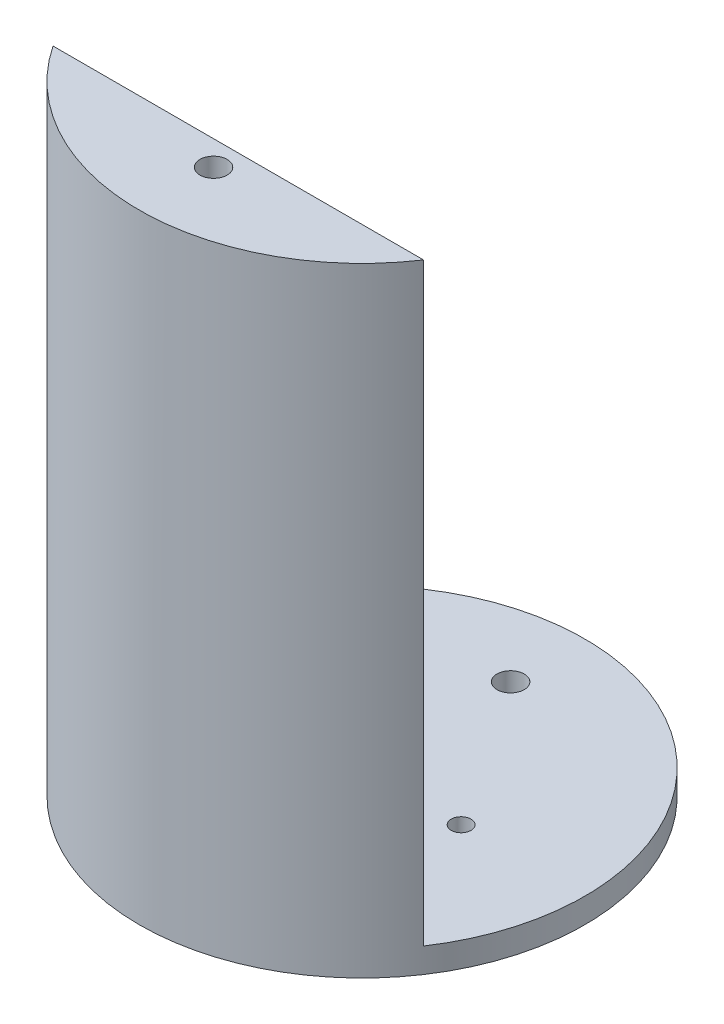
SolidWorks part; units mm, degrees
ref_plane "Front Plane" through (0, 0, 0) normal (0, 0, 1) x (1, 0, 0)
ref_plane "Top Plane" through (0, 0, 0) normal (0, 1, 0) x (1, 0, 0)
ref_plane "Right Plane" through (0, 0, 0) normal (1, 0, 0) x (0, 0, -1)
sketch "Sketch1" plane through (0, 0, 0) normal (0, 1, 0) x (1, 0, 0)
  line L0 (-57.15, 0) -> (57.15, 0)
  arc A0 (-57.15, 0) -> (57.15, 0) centre (0, 0) ccw
  circle A1 centre (0, -38.1) radius 3.4925
  circle A2 centre (0, 0) radius 57.15
  circle A3 centre (0, 38.1) radius 3.4925
  circle A4 centre (0, 0) radius 6.35
  dimension "D1" = 114.3
  dimension "D2" = 6.985
  dimension "D4" = 12.7
  dimension "D3" = 38.1
extrude "Boss-Extrude1" add sketch "Sketch1" along normal blind 6.35 contours L0 A0 A1 | L0 A2 A3
sketch "Sketch2" plane through (0, 6.35, 0) normal (0, 1, 0) x (1, 0, 0)
  line L0 (0, 0) -> (0, -57.15) construction
  line L2 (0, 0) -> (57.15, 0) construction
  circle A0 centre (-25.4, 0) radius 3.175
  circle A3 centre (25.4, 0) radius 3.175
  circle A4 centre (0, 0) radius 57.15 construction
  point P7 (0, -53.1132)
  point P8 (0, 0)
  point P12 (25.4, 0)
  point P13 (0, 0)
  dimension "D1" = 0
  dimension "D3" = 6.35
  dimension "D4" = 6.35
  dimension "D2" = 25.4
  dimension "D5" = 25.4
  dimension "D6" = 0
hole_wizard "#8 (0.199) Diameter Hole1" positions "3DSketch1" profile "Sketch3" hole size "#8" standard "ANSI Inch" end condition through all
sketch3d "3DSketch1"
  point P0 (-25.4, 6.35, 0)
  point P3 (25.4, 6.35, 0)
sketch "Sketch3" plane through (-25.4, 6.35, 0) normal (1, 0, 0) x (0, 0, 1)
  line L0 (0, 0) -> (0, 6.35)
  line L1 (0, 6.35) -> (2.5273, 6.35)
  line L2 (2.5273, 6.35) -> (2.5273, 0)
  line L5 (2.5273, 0) -> (0, 0)
  line L11 (0, -6.35) -> (0, 107.95) construction
  dimension "Thru Hole Dia." = 5.0546
  dimension "Thru Hole Depth" = 6.35
sketch "Sketch6" plane through (0, 6.35, 0) normal (0, 1, 0) x (1, 0, 0)
  line L1 (-47.519, -31.75) -> (47.519, -31.75)
  circle A6 centre (0, -38.1) radius 3.4925 construction
  circle A7 centre (0, -38.1) radius 3.4925
  circle A8 centre (0, 0) radius 57.15 construction
  circle A9 centre (0, 0) radius 57.15
  point P8 (0, 0)
  point P9 (-46.5672, -31.75)
  circle M12 centre (0, -38.1) radius 3.4925
  circle M13 centre (0, 0) radius 57.15
  dimension "D1" = 6.35
extrude "Boss-Extrude3" add sketch "Sketch6" along normal blind 152.4 contours L1 M13 M12
